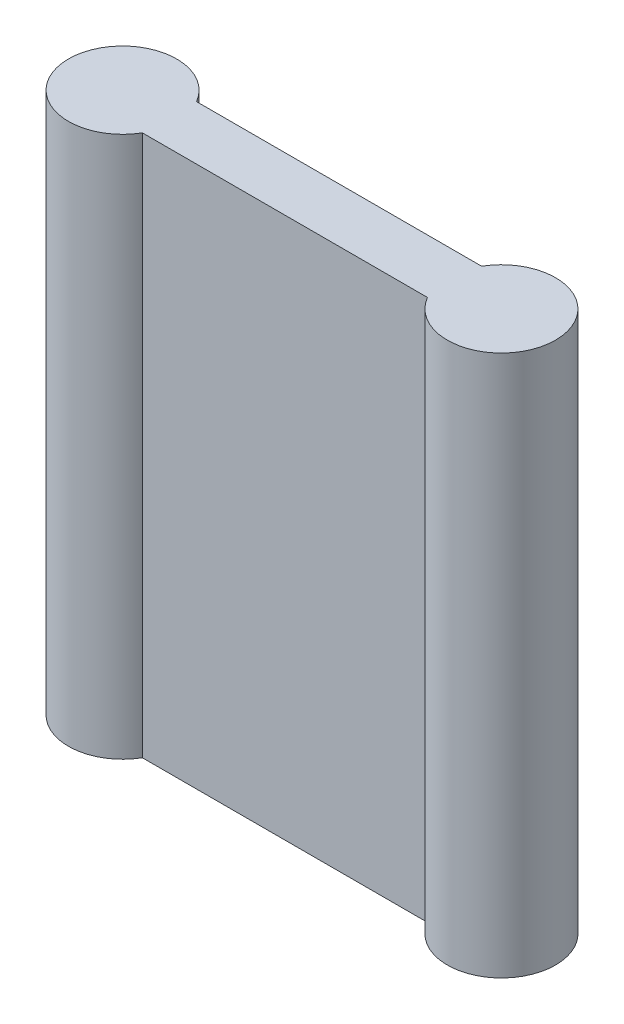
SolidWorks part; units mm, degrees
ref_plane "Front Plane" through (0, 0, 0) normal (0, 0, 1) x (1, 0, 0)
ref_plane "Top Plane" through (0, 0, 0) normal (0, 1, 0) x (1, 0, 0)
ref_plane "Right Plane" through (0, 0, 0) normal (1, 0, 0) x (0, 0, -1)
sketch "Sketch1" plane through (0, 0, 0) normal (0, 0, 1) x (1, 0, 0)
  line L1 (7, 10) -> (-7, 10)
  line L2 (7, 10) -> (7, -10)
  line L3 (7, -10) -> (-7, -10)
  line L4 (-7, 10) -> (-7, -10)
  line L5 (7, 10) -> (-7, -10) construction
  line L6 (7, -10) -> (-7, 10) construction
  point P1 (0, 0)
  dimension "D1" = 14
  dimension "16" = 20
extrude "Boss-Extrude1" add sketch "Sketch1" along normal blind 2
sketch "Sketch4" plane through (0, -10, 0) normal (0, -1, 0) x (1, 0, 0)
  line L0 (-7, 2) -> (-7, 0) construction
  line L1 (7, 2) -> (7, 0) construction
  circle A0 centre (-7, 1) radius 2
  circle A1 centre (7, 1) radius 2
  dimension "D1" = 4
  dimension "D2" = 4
extrude "Boss-Extrude4" add sketch "Sketch4" against normal up to surface (20 mm away) up to face at (0, 10, 1)
